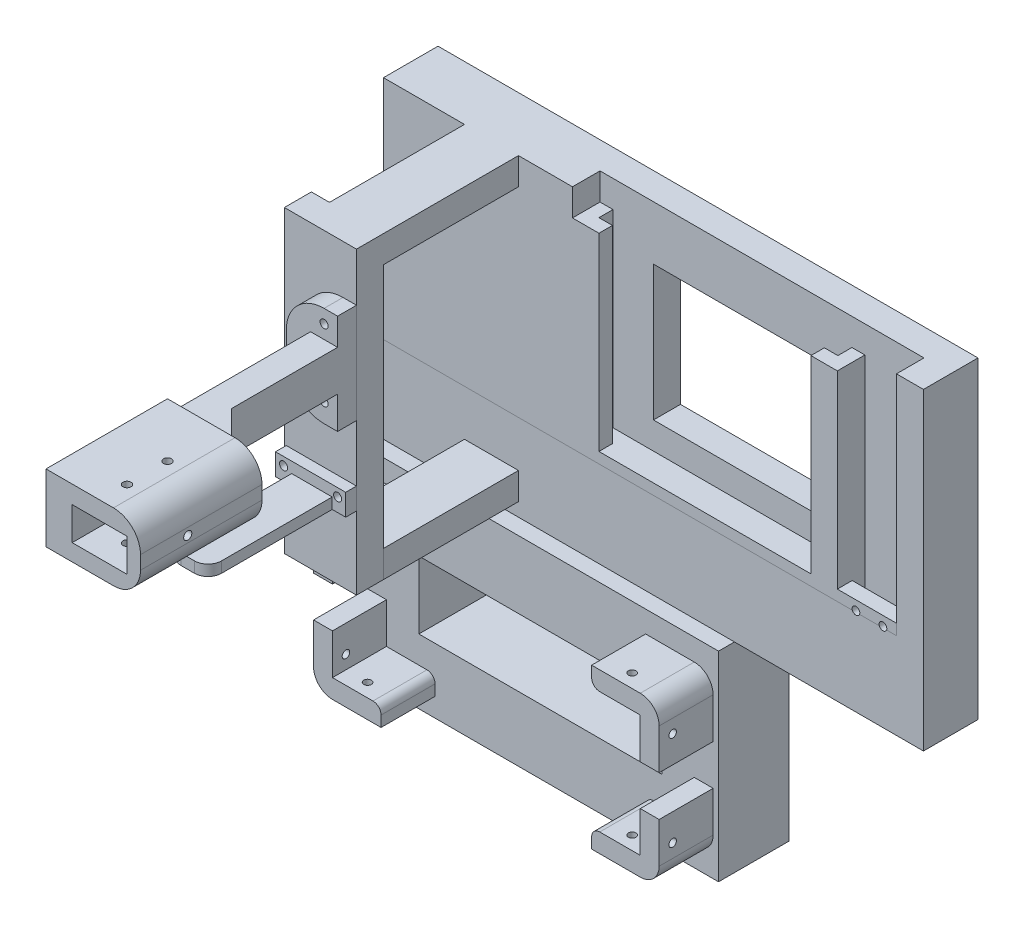
SolidWorks part; units mm, degrees
ref_plane "Front Plane" through (0, 0, 0) normal (0, 0, 1) x (1, 0, 0)
ref_plane "Top Plane" through (0, 0, 0) normal (0, 1, 0) x (1, 0, 0)
ref_plane "Right Plane" through (0, 0, 0) normal (1, 0, 0) x (0, 0, -1)
sketch "Sketch1" plane through (0, 0, 0) normal (0, 0, 1) x (1, 0, 0)
  line L1 (-95, -40) -> (95, -40)
  line L2 (-95, -40) -> (-95, 40)
  line L3 (-95, 40) -> (95, 40)
  line L4 (95, -40) -> (95, 40)
  line L5 (-95, -40) -> (95, 40) construction
  line L6 (-95, 40) -> (95, -40) construction
  point P0 (0, 0)
  dimension "D1" = 0
  dimension "D2" = 190
  dimension "80" = 80
extrude "Boss-Extrude1" add sketch "Sketch1" along normal blind 10
sketch "Sketch2" plane through (0, -40, 0) normal (0, -1, 0) x (1, 0, 0)
  line L0 (-95, 10) -> (95, 10) construction
  line L1 (-25, 10) -> (-20.2, 10)
  line L2 (-25, 10) -> (-25, 15.2)
  line L3 (-25, 15.2) -> (-20.2, 15.2)
  line L4 (-20.2, 10) -> (-20.2, 15.2)
  line L5 (-25, 20.2) -> (-15.2, 20.2)
  line L6 (-25, 20.2) -> (-25, 15.2)
  line L7 (-25, 15.2) -> (-15.2, 15.2)
  line L8 (-15.2, 20.2) -> (-15.2, 15.2)
  line L9 (73.1, 10) -> (68.3, 10)
  line L10 (73.1, 10) -> (73.1, 15.2)
  line L11 (73.1, 15.2) -> (68.3, 15.2)
  line L12 (68.3, 10) -> (68.3, 15.2)
  line L13 (63.3, 20.2) -> (73.1, 20.2)
  line L14 (63.3, 20.2) -> (63.3, 15.2)
  line L15 (63.3, 15.2) -> (73.1, 15.2)
  line L16 (73.1, 20.2) -> (73.1, 15.2)
  line L17 (-95, 10) -> (-95, 0) construction
  dimension "D1" = 0
  dimension "D2" = 0
  dimension "D3" = 0
  dimension "D4" = 5.2
  dimension "D5" = 9.8
  dimension "D6" = 5
  dimension "D7" = 4.8
  dimension "D8" = 9.8
  dimension "D9" = 5
  dimension "D10" = 0
  dimension "D11" = 0
  dimension "D12" = 0
  dimension "D13" = 5.2
  dimension "D14" = 4.8
  dimension "D15" = 88.5
  dimension "D16" = 70
extrude "Boss-Extrude2" add sketch "Sketch2" against normal blind 70 contours L8 L5 L6 L3 L7 | L16 L13 L14 L15 L11
sketch "Sketch3" plane through (0, 0, 10) normal (0, 0, 1) x (1, 0, 0)
  line L0 (-20.2, -40) -> (68.3, -40) construction
  line L1 (53.3, -30) -> (-5.2, -30)
  line L2 (53.3, -30) -> (53.3, 20)
  line L3 (53.3, 20) -> (-5.2, 20)
  line L4 (-5.2, -30) -> (-5.2, 20)
  line L5 (63.3, 30) -> (63.3, -40) construction
  line L6 (-15.2, 30) -> (-15.2, -40) construction
  line L7 (73.1, 30) -> (68.3, 30) construction
  dimension "D1" = 10
  dimension "D2" = 10
  dimension "D3" = 10
  dimension "D4" = 10
extrude "Cut-Extrude1" cut sketch "Sketch3" against normal blind 10
sketch "Sketch5" plane through (0, -40, 0) normal (0, -1, 0) x (-1, 0, 0)
  line L0 (25, -20.2) -> (15.2, -20.2) construction
  line L1 (95, -20.2) -> (-95, -20.2)
  line L2 (95, -20.2) -> (95, 0)
  line L3 (95, 0) -> (-95, 0)
  line L4 (-95, -20.2) -> (-95, 0)
  line L5 (95, -10) -> (95, 0) construction
  line L7 (95, 0) -> (-95, 0) construction
  line L8 (-95, -10) -> (-95, 0) construction
  dimension "D1" = 0
  dimension "D2" = 0
  dimension "D3" = 0
  dimension "D4" = 0
extrude "Boss-Extrude3" add sketch "Sketch5" along normal blind 4
sketch "Sketch6" plane through (0, 0, 0) normal (0, 0, -1) x (-1, 0, 0)
  line L0 (95, -44) -> (-95, -44) construction
  line L1 (95, -44) -> (-95, -44)
  line L2 (95, -44) -> (95, 40)
  line L3 (95, 40) -> (-95, 40)
  line L4 (-95, -44) -> (-95, 40)
  line L5 (95, -150) -> (-105, -150)
  line L6 (95, -150) -> (95, 40)
  line L7 (95, 40) -> (-105, 40)
  line L8 (-105, -150) -> (-105, 40)
  line L9 (95, 40) -> (95, -44) construction
  line L10 (-95, 40) -> (95, 40) construction
  line L11 (-95, -44) -> (-95, 40) construction
  line M5 (-95, 40) -> (-95, -44)
  line M6 (-95, -44) -> (95, -44)
  line M7 (95, -44) -> (95, 40)
  dimension "D1" = 0
  dimension "D2" = 0
  dimension "D3" = 0
  dimension "D4" = 0
  dimension "D5" = 10
  dimension "D6" = 190
  dimension "D7" = 0
  dimension "D8" = 0
extrude "Boss-Extrude5" add sketch "Sketch6" against normal blind 20.1999 contours L8 L5 L6 L7 M7 M6 M5
sketch "Sketch7" plane through (0, 0, 20.1999) normal (0, 0, 1) x (1, 0, 0)
  line L0 (105, -150) -> (105, 40) construction
  line L1 (105, -76) -> (-95, -76)
  line L2 (105, -76) -> (105, -150)
  line L3 (105, -150) -> (-95, -150)
  line L4 (-95, -76) -> (-95, -150)
  line L5 (70.7614, -89.3834) -> (70.4933, -89.3834)
  line L6 (70.7614, -89.3834) -> (70.7614, -108.9872)
  line L7 (70.7614, -108.9872) -> (70.4933, -108.9872)
  line L8 (70.4933, -89.3834) -> (70.4933, -108.9872)
  line L9 (-95, -150) -> (105, -150) construction
  line L10 (-95, -150) -> (-95, -44) construction
  line L11 (95, -44) -> (-95, -44) construction
  dimension "D1" = 0
  dimension "D2" = 0
  dimension "D3" = 0
  dimension "D4" = 32
extrude "Boss-Extrude6" add sketch "Sketch7" along normal blind 5.9
sketch "Sketch21" plane through (0, -40, 0) normal (0, 1, 0) x (1, 0, 0)
  line L0 (95, -10) -> (95, -20.1999) construction
  line L1 (95, -14.7) -> (73.1, -14.7)
  line L2 (95, -14.7) -> (95, -10)
  line L3 (95, -10) -> (73.1, -10)
  line L4 (73.1, -14.7) -> (73.1, -10)
  line L5 (73.1, -10) -> (95, -10) construction
  line L6 (73.1, -20.2) -> (73.1, -10) construction
  dimension "D1" = 0
  dimension "D2" = 0
  dimension "D3" = 4.7
  dimension "D4" = 0
extrude "Cut-Extrude7" cut sketch "Sketch21" against normal blind 5.5
sketch "Sketch22" plane through (0, 0, 20.2) normal (0, 0, 1) x (1, 0, 0)
  line L0 (95, -40) -> (73.1, -40) construction
  line L1 (95, -40) -> (95, -44) construction
  circle A0 centre (90, -43.5) radius 1.425
  circle A1 centre (80, -43.5) radius 1.425
  dimension "D1" = 2.85
  dimension "D2" = 2.85
  dimension "D4" = 3.5
  dimension "D3" = 3.5
  dimension "D5" = 5
  dimension "D6" = 10
extrude "Cut-Extrude8" cut sketch "Sketch22" against normal blind 5.5
sketch "Sketch23" plane through (0, 0, 10) normal (0, 0, 1) x (1, 0, 0)
  line L0 (-25, 30) -> (-25, -40) construction
  line L1 (-25, -40) -> (-95, -40)
  line L2 (-25, -40) -> (-25, 40)
  line L3 (-25, 40) -> (-95, 40)
  line L4 (-95, -40) -> (-95, 40)
  line L5 (-95, -40) -> (-25, -40) construction
  line L6 (-95, 40) -> (-95, -40) construction
  line L7 (95, 40) -> (-95, 40) construction
  dimension "D1" = 0
  dimension "D2" = 0
  dimension "D3" = 0
  dimension "D4" = 0
extrude "Boss-Extrude8" add sketch "Sketch23" along normal blind 10.2
sketch "Sketch24" plane through (0, 0, 26.0999) normal (0, 0, 1) x (1, 0, 0)
  line L0 (105, -150) -> (105, -76) construction
  line L1 (105, -150) -> (35, -150)
  line L2 (105, -150) -> (105, -76)
  line L3 (105, -76) -> (35, -76)
  line L4 (35, -150) -> (35, -76)
  line L5 (105, -76) -> (-95, -76) construction
  line L6 (-95, -150) -> (105, -150) construction
  dimension "D1" = 0
  dimension "D2" = 0
  dimension "D3" = 0
  dimension "D4" = 70
extrude "Cut-Extrude9" cut sketch "Sketch24" against normal through all
sketch "Sketch25" plane through (0, 0, 20.2) normal (0, 0, 1) x (1, 0, 0)
  line L0 (35, -76) -> (-95, -76) construction
  line L1 (-45, 40) -> (-65, 40)
  line L2 (-45, 40) -> (-45, 30)
  line L3 (-45, 30) -> (-65, 30)
  line L4 (-65, 40) -> (-65, 30)
  line L5 (-58, 30) -> (-65, 30)
  line L9 (-25, 40) -> (-95, 40) construction
  line L10 (-95, -44) -> (-95, 40) construction
  line L13 (-45, -71) -> (-65, -71)
  line L14 (-45, -71) -> (-45, -61)
  line L15 (-45, -61) -> (-65, -61)
  line L16 (-65, -71) -> (-65, -61)
  dimension "D2" = 20
  dimension "D3" = 0
  dimension "D4" = 30
  dimension "D5" = 0
  dimension "D6" = 30
  dimension "D7" = 5
  dimension "D11" = 10
  dimension "D12" = 20
  dimension "D13" = 10
extrude "Boss-Extrude10" add sketch "Sketch25" along normal blind 50
sketch "Sketch26" plane through (0, 0, 70.2) normal (0, 0, 1) x (1, 0, 0)
  line L0 (-45, -71) -> (-65, -71) construction
  line L1 (-45, -71) -> (-71.7045, -71)
  line L2 (-45, -71) -> (-45, 40)
  line L3 (-45, 40) -> (-71.7045, 40)
  line L4 (-71.7045, -71) -> (-71.7045, 40)
  line L5 (-45, -71) -> (-45, -61) construction
  dimension "D1" = 0
  dimension "D2" = 0
extrude "Boss-Extrude11" add sketch "Sketch26" along normal blind 10
sketch "Sketch29" plane through (0, 0, 26.0999) normal (0, 0, 1) x (1, 0, 0)
  line L0 (35, -76) -> (-95, -76) construction
  line L1 (-70, -84) -> (-95, -84)
  line L2 (-70, -84) -> (-70, -91)
  line L3 (-70, -91) -> (-95, -91)
  line L4 (-95, -84) -> (-95, -91)
  line L5 (33, -84) -> (8, -84)
  line L6 (33, -84) -> (33, -91)
  line L7 (33, -91) -> (8, -91)
  line L8 (8, -84) -> (8, -91)
  line L9 (-88, -91) -> (-95, -91)
  line L10 (-88, -91) -> (-88, -106)
  line L11 (-88, -106) -> (-95, -106)
  line L12 (-95, -91) -> (-95, -106)
  line L13 (33, -91) -> (26, -91)
  line L14 (33, -91) -> (33, -106)
  line L15 (33, -106) -> (26, -106)
  line L16 (26, -91) -> (26, -106)
  line L17 (33, -121) -> (26, -121)
  line L18 (33, -121) -> (33, -136)
  line L19 (33, -136) -> (26, -136)
  line L20 (26, -121) -> (26, -136)
  line L21 (33, -143) -> (8, -143)
  line L22 (33, -143) -> (33, -136)
  line L23 (33, -136) -> (8, -136)
  line L24 (8, -143) -> (8, -136)
  line L25 (-88, -121) -> (-95, -121)
  line L26 (-88, -121) -> (-88, -136)
  line L27 (-88, -136) -> (-95, -136)
  line L28 (-95, -121) -> (-95, -136)
  line L29 (-95, -136) -> (-70, -136)
  line L30 (-95, -136) -> (-95, -143)
  line L31 (-95, -143) -> (-70, -143)
  line L32 (-70, -136) -> (-70, -143)
  line L34 (35, -76) -> (-95, -76) construction
  line L35 (-95, -76) -> (-95, -150) construction
  dimension "D2" = 15
  dimension "D3" = 7
  dimension "D4" = 25
  dimension "D5" = 0
  dimension "D6" = 7
  dimension "D7" = 0
  dimension "D8" = 0
  dimension "D9" = 15
  dimension "D10" = 7
  dimension "D11" = 25
  dimension "D12" = 0
  dimension "D13" = 0
  dimension "D14" = 114
  dimension "D15" = 7
  dimension "D16" = 15
  dimension "D17" = 7
  dimension "D18" = 0
  dimension "D19" = 0
  dimension "D20" = 7
  dimension "D21" = 15
  dimension "D22" = 114
  dimension "D23" = 0
  dimension "D24" = 0
  dimension "D25" = 7
  dimension "D26" = 7
  dimension "D27" = 15
  dimension "D28" = 0
  dimension "D29" = 45
  dimension "D30" = 25
  dimension "D31" = 25
  dimension "D32" = 45
  dimension "D33" = 15
extrude "Boss-Extrude12" add sketch "Sketch29" along normal blind 20
sketch "Sketch30" plane through (0, -143, 0) normal (0, -1, 0) x (1, 0, 0)
  line L0 (33, 26.0999) -> (8, 26.0999) construction
  line L1 (33, 46.0999) -> (33, 26.0999) construction
  line L2 (-95, 26.0999) -> (-70, 26.0999) construction
  line L3 (-95, 46.0999) -> (-95, 26.0999) construction
  circle A0 centre (18, 41.0999) radius 1.4
  circle A1 centre (-80, 41.0999) radius 1.4
  dimension "D1" = 2.8
  dimension "D2" = 15
  dimension "D3" = 15
  dimension "D4" = 2.8
  dimension "D5" = 15
  dimension "D6" = 15
extrude "Cut-Extrude12" cut sketch "Sketch30" against normal blind 60
sketch "Sketch31" plane through (-95, 0, 0) normal (-1, 0, 0) x (0, 0, 1)
  line L0 (46.0999, -106) -> (26.0999, -106) construction
  line L1 (26.0999, -106) -> (26.0999, -121) construction
  line L2 (46.0999, -121) -> (26.0999, -121) construction
  circle A0 centre (41.0999, -96) radius 1.4
  circle A1 centre (41.0999, -131) radius 1.4
  dimension "D1" = 2.8
  dimension "D2" = 10
  dimension "D3" = 15
  dimension "D4" = 15
  dimension "D5" = 2.8
  dimension "D6" = 10
extrude "Cut-Extrude13" cut sketch "Sketch31" against normal blind 129
sketch "Sketch32" plane through (0, 0, 26.0999) normal (0, 0, 1) x (1, 0, 0)
  line L0 (-88, -91) -> (-88, -106) construction
  line L1 (-76, -101) -> (14, -101)
  line L2 (-76, -101) -> (-76, -126)
  line L3 (-76, -126) -> (14, -126)
  line L4 (14, -101) -> (14, -126)
  line L5 (26, -91) -> (26, -106) construction
  line L6 (26, -91) -> (8, -91) construction
  line L7 (-88, -136) -> (-70, -136) construction
  dimension "D1" = 12
  dimension "D2" = 12
  dimension "D3" = 10
  dimension "D4" = 10
extrude "Cut-Extrude14" cut sketch "Sketch32" against normal blind 129
fillet "Fillet1" radius 7 1 edges at (-95, -143, 36.0999)
fillet "Fillet2" radius 7 1 edges at (-95, -84, 36.0999)
fillet "Fillet3" radius 7 1 edges at (33, -143, 36.0999)
fillet "Fillet4" radius 7 1 edges at (33, -84, 36.0999)
fillet "Fillet5" radius 3 1 edges at (-70, -91, 36.0999)
fillet "Fillet6" radius 3 1 edges at (-70, -136, 36.0999)
fillet "Fillet7" radius 3 1 edges at (8, -91, 36.0999)
fillet "Fillet8" radius 3 1 edges at (8, -136, 36.0999)
sketch "Sketch33" plane through (0, 0, 80.2) normal (0, 0, 1) x (1, 0, 0)
  line L0 (-45, -71) -> (-45, 40) construction
  line L1 (-50, -44) -> (-65, -44)
  line L2 (-50, -44) -> (-50, -40)
  line L3 (-50, -40) -> (-65, -40)
  line L4 (-65, -44) -> (-65, -40)
  line L5 (-71.7045, -71) -> (-45, -71) construction
  dimension "D1" = 5
  dimension "D2" = 15
  dimension "D3" = 4
  dimension "D4" = 27
extrude "Boss-Extrude13" add sketch "Sketch33" along normal blind 50
sketch "Sketch36" plane through (0, 0, 80.2) normal (0, 0, 1) x (1, 0, 0)
  line L0 (-45, 40) -> (-71.7045, 40) construction
  line L1 (-45, -3) -> (-55, -3)
  line L2 (-45, -3) -> (-45, 12)
  line L3 (-45, 12) -> (-55, 12)
  line L4 (-55, -3) -> (-55, 12)
  line L5 (-45, -71) -> (-45, 40) construction
  dimension "D1" = 28
  dimension "D2" = 15
  dimension "D3" = 0
  dimension "D4" = 10
extrude "Boss-Extrude15" add sketch "Sketch36" along normal blind 60
sketch "Sketch37" plane through (0, 0, 140.2) normal (0, 0, 1) x (1, 0, 0)
  line L0 (-45, 12) -> (-55, 12) construction
  line L1 (-55, 17) -> (-20, 17)
  line L2 (-55, 17) -> (-55, -8)
  line L3 (-55, -8) -> (-20, -8)
  line L4 (-20, 17) -> (-20, -8)
  line L5 (-55, 12) -> (-55, -3) construction
  dimension "D1" = 5
  dimension "D2" = 25
  dimension "D3" = 0
  dimension "D4" = 35
extrude "Boss-Extrude16" add sketch "Sketch37" along normal blind 10
sketch "Sketch38" plane through (0, 0, 150.2) normal (0, 0, 1) x (1, 0, 0)
  line L0 (-55, -8) -> (-20, -8) construction
  line L1 (-20, -8) -> (-55, -8)
  line L2 (-20, -8) -> (-20, 17)
  line L3 (-20, 17) -> (-55, 17)
  line L4 (-55, -8) -> (-55, 17)
  line L5 (-25, -1.8) -> (-45.3, -1.8)
  line L6 (-25, -1.8) -> (-25, 10.4)
  line L7 (-25, 10.4) -> (-45.3, 10.4)
  line L8 (-45.3, -1.8) -> (-45.3, 10.4)
  line L9 (-20, -8) -> (-20, 17) construction
  line L10 (-20, 17) -> (-55, 17) construction
  line L11 (-55, 17) -> (-55, -8) construction
  dimension "D1" = 0
  dimension "D2" = 0
  dimension "D3" = 0
  dimension "D4" = 20.3
  dimension "0" = 0
  dimension "D5" = 12.2
  dimension "D6" = 5
  dimension "D7" = 6.6
extrude "Boss-Extrude17" add sketch "Sketch38" along normal blind 35
sketch "Sketch39" plane through (0, 17, 0) normal (0, 1, 0) x (1, 0, 0)
  line L0 (-45.3, -150.2) -> (-25, -150.2) construction
  line L1 (-20, -185.2) -> (-20, -140.2) construction
  circle A0 centre (-35, -160.2) radius 1.5
  circle A1 centre (-35, -175.2) radius 1.5
  dimension "D1" = 10
  dimension "D2" = 3
  dimension "D3" = 3
  dimension "D4" = 25
  dimension "D5" = 15
  dimension "D6" = 15
extrude "Cut-Extrude15" cut sketch "Sketch39" against normal blind 30
sketch "Sketch40" plane through (-20, 0, 0) normal (1, 0, 0) x (0, 0, -1)
  line L0 (-140.2, -8) -> (-140.2, 17) construction
  line L1 (-185.2, 17) -> (-140.2, 17) construction
  circle A0 centre (-167.7, 4.4) radius 1.5
  dimension "D1" = 3
  dimension "D2" = 27.5
  dimension "D3" = 12.6
extrude "Cut-Extrude16" cut sketch "Sketch40" against normal blind 49
sketch "Sketch41" plane through (0, 12, 0) normal (0, 1, 0) x (1, 0, 0)
  line L0 (-45, -136.547) -> (-45, -126.547)
  line L1 (-45, -126.547) -> (-31.347, -140.2)
  line L2 (-31.347, -140.2) -> (-41.347, -140.2)
  line L3 (-41.347, -140.2) -> (-45, -136.547)
  line L5 (-20, -140.2) -> (-55, -140.2) construction
  line L7 (-45, -80.2) -> (-45, -140.2) construction
  dimension "D1" = 0
  dimension "D2" = 0
  dimension "D3" = 0
  dimension "D4" = 10
  dimension "D5" = 10
extrude "Boss-Extrude18" add sketch "Sketch41" against normal up to surface (15 mm away) up to face at (-51.25, -3, 117.7)
sketch "Sketch42" plane through (0, 12, 0) normal (0, 1, 0) x (1, 0, 0)
  line L0 (-45, -80.2) -> (-55, -80.2) construction
  line L1 (-45, -87.2) -> (-64, -87.2)
  line L2 (-45, -87.2) -> (-45, -80.2)
  line L3 (-45, -80.2) -> (-64, -80.2)
  line L4 (-64, -87.2) -> (-64, -80.2)
  line L5 (-55, -80.2) -> (-55, -140.2) construction
  line L6 (-45, -80.2) -> (-45, -126.547) construction
  dimension "D1" = 0
  dimension "D2" = 7
  dimension "D3" = 9
  dimension "D4" = 0
extrude "Boss-Extrude19" add sketch "Sketch42" along normal blind 10 and the other way blind 27
sketch "Sketch43" plane through (0, 0, 87.2) normal (0, 0, 1) x (1, 0, 0)
  line L0 (-55, -3) -> (-55, 12) construction
  line L1 (-55, 12) -> (-45, 12) construction
  line L2 (-45, -3) -> (-55, -3) construction
  line L3 (-45, -15) -> (-45, -3) construction
  line L4 (-45, 12) -> (-45, 22) construction
  circle A0 centre (-50, 17) radius 1.5
  circle A1 centre (-50, -8) radius 1.5
  circle A2 centre (-60, 4.5) radius 1.5
  dimension "D1" = 3
  dimension "D2" = 3
  dimension "D3" = 3
  dimension "D4" = 5
  dimension "D5" = 5
  dimension "D6" = 5
  dimension "D7" = 5
  dimension "D8" = 5
  dimension "D9" = 7.5
fillet "Fillet9" radius 14 1 edges at (-64, 22, 83.7)
fillet "Fillet10" radius 14 1 edges at (-64, -15, 83.7)
extrude "Cut-Extrude17" cut sketch "Sketch43" against normal blind 30
sketch "Sketch44" plane through (-50, 0, 0) normal (1, 0, 0) x (0, 0, -1)
  line L0 (-80.2, -44) -> (-80.2, -40) construction
  line L1 (-84.2, -44) -> (-80.2, -44)
  line L2 (-84.2, -44) -> (-84.2, -36)
  line L3 (-84.2, -36) -> (-80.2, -36)
  line L4 (-80.2, -44) -> (-80.2, -36)
  line L5 (-130.2, -44) -> (-80.2, -44) construction
  dimension "D1" = 0
  dimension "D2" = 0
  dimension "D3" = 4
  dimension "D4" = 8
extrude "Boss-Extrude20" add sketch "Sketch44" along normal up to surface (5 mm away) and the other way blind 21 up to face at (-45, -8.75, 61.0333)
sketch "Sketch45" plane through (0, 0, 84.2) normal (0, 0, 1) x (1, 0, 0)
  line L0 (-45, -36) -> (-45, -44) construction
  line L1 (-71, -44) -> (-45, -44) construction
  line L4 (-71, -36) -> (-71, -44) construction
  circle A0 centre (-48, -39) radius 1.5
  circle A2 centre (-68, -39) radius 1.5
  dimension "D1" = 3
  dimension "D2" = 3
  dimension "D3" = 3
  dimension "D4" = 5
  dimension "D5" = 5
  dimension "D7" = 3
extrude "Cut-Extrude18" cut sketch "Sketch45" against normal blind 20
fillet "Fillet11" radius 5 1 edges at (-65, -42, 130.2)
fillet "Fillet12" radius 5 1 edges at (-50, -42, 130.2)
fillet "Fillet16" radius 10 1 edges at (-20, -8, 162.7)
fillet "Fillet15" radius 10 1 edges at (-20, 17, 162.7)
split "Split1" bodies to split 158 resulting bodies 181
